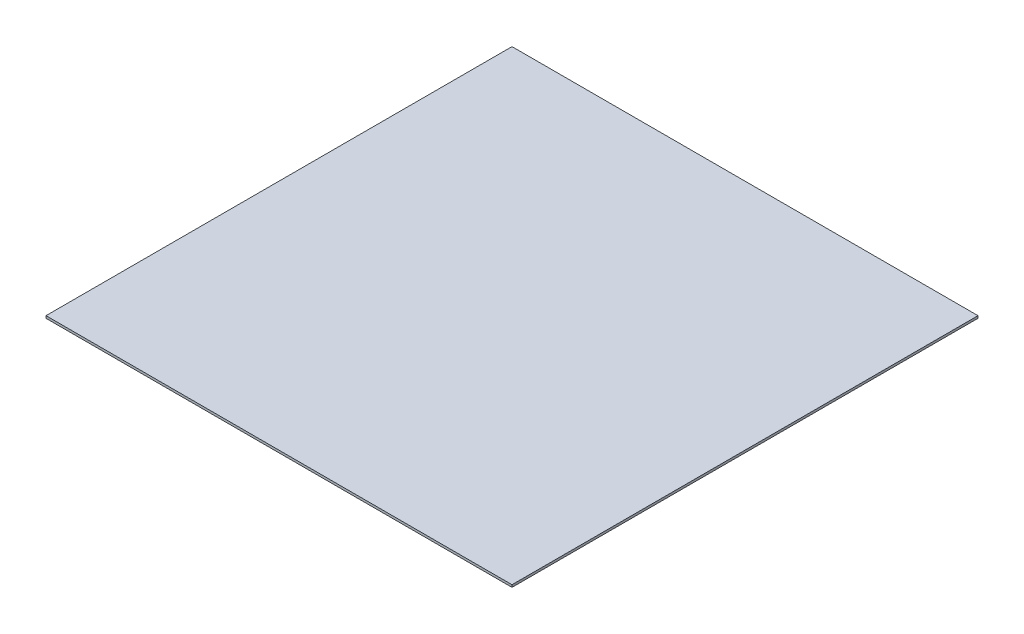
SolidWorks part; units mm, degrees
ref_plane "Front Plane" through (0, 0, 0) normal (0, 0, 1) x (1, 0, 0)
ref_plane "Top Plane" through (0, 0, 0) normal (0, 1, 0) x (1, 0, 0)
ref_plane "Right Plane" through (0, 0, 0) normal (1, 0, 0) x (0, 0, -1)
sketch "Sketch1" plane through (0, 0, 0) normal (0, 1, 0) x (1, 0, 0)
  line L1 (-1000, 1000) -> (1000, 1000)
  line L2 (-1000, 1000) -> (-1000, -1000)
  line L3 (-1000, -1000) -> (1000, -1000)
  line L4 (1000, 1000) -> (1000, -1000)
  line L5 (-1000, 1000) -> (1000, -1000) construction
  line L6 (-1000, -1000) -> (1000, 1000) construction
  point P0 (0, 0)
  dimension "D1" = 2000
  dimension "D2" = 2000
extrude "Boss-Extrude1" add sketch "Sketch1" along normal blind 10
